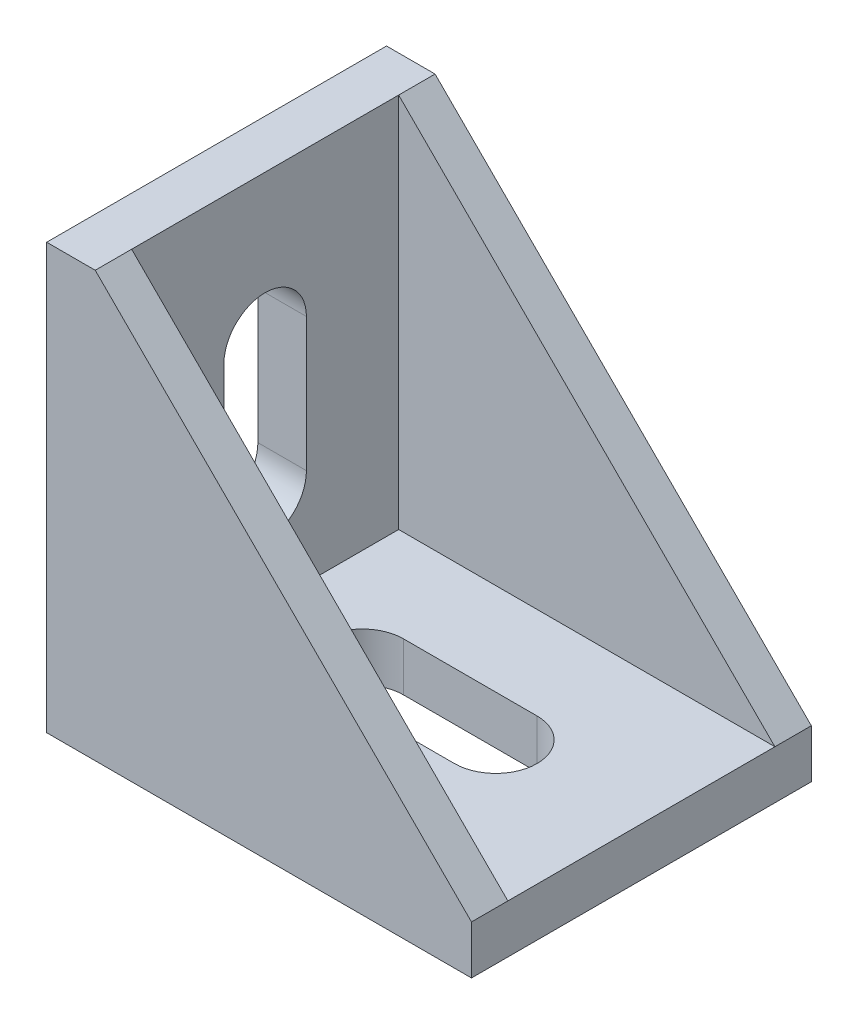
SolidWorks part; units mm, degrees
material "Алюминиевый сплав"
ref_plane "Спереди" through (0, 0, 0) normal (0, 0, 1) x (1, 0, 0)
ref_plane "Сверху" through (0, 0, 0) normal (0, 1, 0) x (1, 0, 0)
ref_plane "Справа" through (0, 0, 0) normal (1, 0, 0) x (0, 0, -1)
sketch "Эскиз1" plane through (0, 0, 0) normal (0, 0, 1) x (1, 0, 0)
  line L0 (0, 35) -> (0, 0)
  line L1 (0, 0) -> (35, 0)
  line L2 (35, 0) -> (35, 4)
  line L4 (4, 35) -> (0, 35)
  line L5 (4, 35) -> (4, 4)
  line L6 (4, 4) -> (35, 4)
  dimension "D1" = 35
  dimension "D2" = 4
extrude "Бобышка-Вытянуть1" add sketch "Эскиз1" along normal mid plane 28
sketch "Эскиз2" plane through (0, 0, 14) normal (0, 0, 1) x (1, 0, 0)
  line L0 (4, 35) -> (35, 4)
  line L1 (35, 4) -> (4, 4)
  line L2 (4, 4) -> (4, 35)
extrude "Бобышка-Вытянуть2" add sketch "Эскиз2" against normal blind 3
mirror "Зеркальное отражение2" about plane through (0, 0, 0) normal (0, 0, 1) of "Бобышка-Вытянуть2"
sketch "Эскиз3" plane through (0, 4, 0) normal (0, 1, 0) x (1, 0, 0)
  line L0 (12, 0) -> (23, 0) construction
  line L1 (12, 3.4) -> (23, 3.4)
  line L2 (12, -3.4) -> (23, -3.4)
  line L3 (0, -14) -> (0, 14) construction
  arc A0 (12, 3.4) -> (12, -3.4) centre (12, 0) ccw
  arc A1 (23, -3.4) -> (23, 3.4) centre (23, 0) ccw
  point P2 (17.5, 0)
  dimension "D2" = 3.4
  dimension "D3" = 12
  dimension "D1" = 11
extrude "Вырез-Вытянуть1" cut sketch "Эскиз3" against normal through all
sketch "Эскиз4" plane through (0, 0, 0) normal (0, -1, 0) x (1, 0, 0)
  line L0 (0, 14) -> (0, -14) construction
  line L1 (3, -4) -> (5.5, -4)
  line L2 (3, -4) -> (3, 4)
  line L3 (3, 4) -> (5.5, 4)
  line L4 (5.5, -4) -> (5.5, 4)
  line L5 (3, -4) -> (5.5, 4) construction
  line L6 (3, 4) -> (5.5, -4) construction
  line L7 (29.5, -4) -> (32, -4)
  line L8 (29.5, -4) -> (29.5, 4)
  line L9 (29.5, 4) -> (32, 4)
  line L10 (32, -4) -> (32, 4)
  line L11 (29.5, -4) -> (32, 4) construction
  line L12 (29.5, 4) -> (32, -4) construction
  line L13 (35, 14) -> (35, -14) construction
  point P0 (4.25, 0)
  point P5 (30.75, 0)
  dimension "D1" = 3
  dimension "D2" = 2.5
  dimension "D3" = 8
  dimension "D4" = 3
extrude "Бобышка-Вытянуть3" add sketch "Эскиз4" along normal blind 2.5
ref_plane "Плоскость1" through (0, 0, 0) normal (-0.7071, 0.7071, 0) x (0.7071, 0.7071, 0)
mirror "Зеркальное отражение3" about plane through (0, 0, 0) normal (-0.7071, 0.7071, 0) of "Бобышка-Вытянуть3", "Вырез-Вытянуть1"
